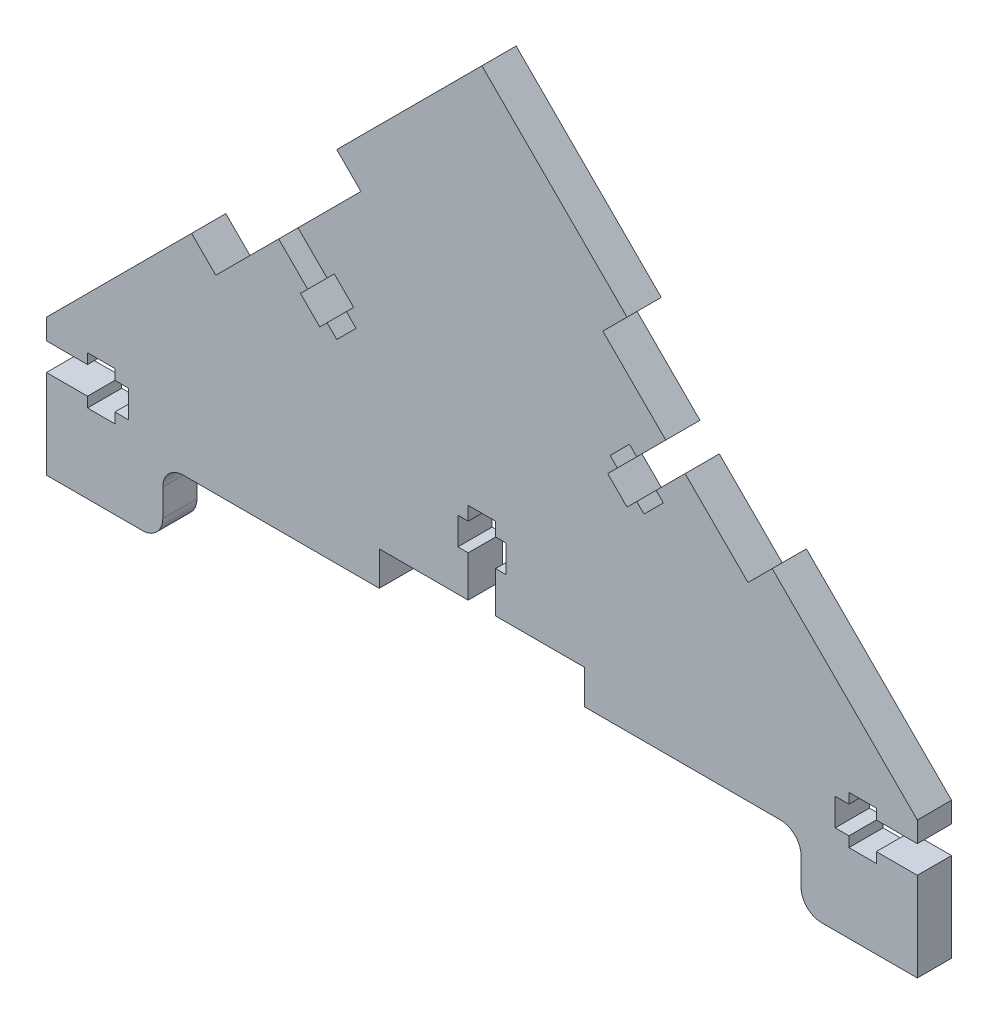
SolidWorks part; units mm, degrees
ref_plane "Front Plane" through (0, 0, 0) normal (0, 0, 1) x (1, 0, 0)
ref_plane "Top Plane" through (0, 0, 0) normal (0, 1, 0) x (1, 0, 0)
ref_plane "Right Plane" through (0, 0, 0) normal (1, 0, 0) x (0, 0, -1)
sketch "Sketch1" plane through (0, 0, 0) normal (0, 0, 1) x (1, 0, 0)
  line L0 (0, 0) -> (127.2792, 0)
  line L1 (0, 0) -> (0, 10)
  line L2 (0, 10) -> (21.2132, 31.2132)
  line L3 (63.6396, 73.6396) -> (84.8528, 52.4264)
  line L4 (84.8528, 52.4264) -> (81.3173, 48.8909)
  line L5 (106.066, 31.2132) -> (102.5305, 27.6777)
  line L6 (60.8931, 7.2535) -> (133.3872, 79.7476) construction
  line L7 (81.3173, 48.8909) -> (102.5305, 27.6777)
  line L8 (106.066, 31.2132) -> (127.2792, 10)
  line L9 (60.1041, 70.1041) -> (184.361, -54.1529) construction
  line L10 (127.2792, 10) -> (127.2792, 0)
  line L11 (63.6396, 73.6396) -> (187.8966, -50.6173) construction
  line L12 (0, 10) -> (0, 100.6449) construction
  line L13 (6.4796, 67.16) -> (53.2637, 20.3759) construction
  line L14 (21.2132, 31.2132) -> (24.7487, 27.6777)
  line L15 (42.4264, 52.4264) -> (63.6396, 73.6396)
  line L17 (42.4264, 52.4264) -> (45.9619, 48.8909)
  line L20 (-4.127, 56.5534) -> (42.6571, 9.7693) construction
  line L24 (24.7487, 27.6777) -> (45.9619, 48.8909)
  point P21 (-6.1493, 65.5118)
  point P22 (51.1493, 32.4305)
  point P23 (4.3301, 7.5)
  point P24 (34.3301, 59.4615)
  dimension "D1" = 10
  dimension "D2" = 45
  dimension "D3" = 90
  dimension "D4" = 45
  dimension "D6" = 15
  dimension "D7" = 15
  dimension "D8" = 10
  dimension "D9" = 15
  dimension "D10" = 15
  dimension "D11" = 5
  dimension "D12" = 30
  dimension "D13" = 45
  dimension "D5" = 5
extrude "Boss-Extrude1" add sketch "Sketch1" along normal blind 5
sketch "Sketch2" plane through (0, 0, 5) normal (0, 0, 1) x (1, 0, 0)
  line L0 (0, 5) -> (61.6396, 5) construction
  line L1 (0, 10) -> (0, 0) construction
  line L2 (127.2792, 0) -> (127.2792, 10) construction
  line L3 (36.8406, 5) -> (99.4047, 5) construction
  line L4 (127.2792, 3) -> (121.2792, 3)
  line L5 (121.2792, 3) -> (121.2792, 1.5)
  line L6 (121.2792, 1.5) -> (117.2792, 1.5)
  line L7 (117.2792, 1.5) -> (117.2792, 3)
  line L8 (117.2792, 3) -> (115.2792, 3)
  line L9 (115.2792, 3) -> (115.2792, 7)
  line L10 (115.2792, 7) -> (117.2792, 7)
  line L11 (117.2792, 7) -> (117.2792, 8.5)
  line L12 (117.2792, 8.5) -> (121.2792, 8.5)
  line L13 (121.2792, 8.5) -> (121.2792, 7)
  line L14 (121.2792, 7) -> (127.2792, 7)
  line L15 (127.2792, 7) -> (127.2792, 3)
  line L16 (36.7696, 39.6985) -> (33.9411, 36.8701)
  line L17 (63.6396, 73.6396) -> (63.6396, -29.0488) construction
  line L18 (0, 7) -> (0, 3)
  line L19 (6, 7) -> (0, 7)
  line L20 (6, 8.5) -> (6, 7)
  line L21 (10, 8.5) -> (6, 8.5)
  line L22 (10, 7) -> (10, 8.5)
  line L23 (12, 7) -> (10, 7)
  line L24 (12, 3) -> (12, 7)
  line L25 (10, 3) -> (12, 3)
  line L26 (10, 1.5) -> (10, 3)
  line L27 (6, 1.5) -> (10, 1.5)
  line L28 (6, 3) -> (6, 1.5)
  line L29 (0, 3) -> (6, 3)
  line L30 (63.6396, 5) -> (63.6396, 17) construction
  line L31 (48.6396, 5) -> (61.6396, 5)
  line L32 (48.6396, 5) -> (48.6396, 0)
  line L33 (48.6396, 0) -> (78.6396, 0)
  line L34 (43.8406, 32.6274) -> (44.9013, 33.6881)
  line L35 (45.2548, 31.2132) -> (43.8406, 32.6274)
  line L36 (42.4264, 28.3848) -> (45.2548, 31.2132)
  line L37 (78.6396, 5) -> (78.6396, 0)
  line L38 (48.6396, 5) -> (78.6396, 0) construction
  line L39 (48.6396, 0) -> (78.6396, 5) construction
  line L40 (61.6396, 5) -> (61.6396, 11)
  line L41 (61.6396, 11) -> (60.1396, 11)
  line L42 (35.3553, 38.2843) -> (43.8406, 29.799) construction
  line L43 (0, 0) -> (127.2792, 0) construction
  line L44 (60.1396, 11) -> (60.1396, 15)
  line L45 (36.7696, 39.6985) -> (41.0122, 35.4558)
  line L46 (41.0122, 35.4558) -> (42.0729, 36.5165)
  line L47 (42.0729, 36.5165) -> (44.9013, 33.6881)
  line L48 (60.1396, 15) -> (61.6396, 15)
  line L49 (61.6396, 15) -> (61.6396, 17)
  line L50 (42.4264, 28.3848) -> (41.0122, 29.799)
  line L51 (41.0122, 29.799) -> (39.9515, 28.7383)
  line L52 (39.9515, 28.7383) -> (37.1231, 31.5668)
  line L53 (37.1231, 31.5668) -> (38.1838, 32.6274)
  line L54 (38.1838, 32.6274) -> (33.9411, 36.8701)
  line L55 (91.9239, 38.2843) -> (83.4386, 29.799) construction
  line L56 (61.6396, 17) -> (65.6396, 17)
  line L57 (65.6396, 17) -> (65.6396, 15)
  line L58 (65.6396, 15) -> (67.1396, 15)
  line L59 (67.1396, 15) -> (67.1396, 11)
  line L60 (67.1396, 11) -> (65.6396, 11)
  line L61 (65.6396, 11) -> (65.6396, 5)
  line L63 (65.6396, 5) -> (78.6396, 5)
  line L64 (65.6396, 5) -> (127.2792, 5) construction
  line L66 (93.3381, 36.8701) -> (89.0955, 32.6274)
  line L67 (89.0955, 32.6274) -> (90.1561, 31.5668)
  line L68 (90.1561, 31.5668) -> (87.3277, 28.7383)
  line L69 (87.3277, 28.7383) -> (86.267, 29.799)
  line L70 (86.267, 29.799) -> (84.8528, 28.3848)
  line L71 (84.8528, 28.3848) -> (82.0244, 31.2132)
  line L72 (82.0244, 31.2132) -> (83.4386, 32.6274)
  line L73 (83.4386, 32.6274) -> (82.3779, 33.6881)
  line L74 (82.3779, 33.6881) -> (85.2064, 36.5165)
  line L75 (85.2064, 36.5165) -> (86.267, 35.4558)
  line L76 (86.267, 35.4558) -> (90.5097, 39.6985)
  line L77 (90.5097, 39.6985) -> (93.3381, 36.8701)
  point P12 (127.2792, 5)
  point P21 (115.2792, 5)
  point P37 (63.6396, 2.5)
  dimension "D1" = 12
  dimension "D2" = 6
  dimension "D3" = 4
  dimension "D4" = 1.5
  dimension "D5" = 4
  dimension "D6" = 0
  dimension "D7" = 5
  dimension "D8" = 30
  dimension "D9" = 4
  dimension "D10" = 3.5
  dimension "D11" = 3.5
  dimension "D12" = 2
  dimension "D13" = 2
extrude "Cut-Extrude1" cut sketch "Sketch2" against normal blind 10
sketch "Sketch4" plane through (0, 0, 5) normal (0, 0, 1) x (1, 0, 0)
  line L1 (0, 0) -> (17, 0)
  line L2 (0, 0) -> (0, -10)
  line L3 (0, -10) -> (17, -10)
  line L4 (17, 0) -> (17, -10)
  line L5 (127.2792, 0) -> (110.2792, 0)
  line L6 (127.2792, 0) -> (127.2792, -10)
  line L7 (127.2792, -10) -> (110.2792, -10)
  line L8 (110.2792, 0) -> (110.2792, -10)
  dimension "D1" = 10
  dimension "D2" = 17
  dimension "D3" = 10
extrude "Boss-Extrude3" add sketch "Sketch4" against normal blind 5
fillet "Fillet1" radius 3 4 edges at (17, -10, 2.5) (17, 0, 2.5) (110.2792, -10, 2.5) (110.2792, 0, 2.5)
equation "\"slot\"= \"lenght\" / \"A\""
equation "\"A\"= 4"
